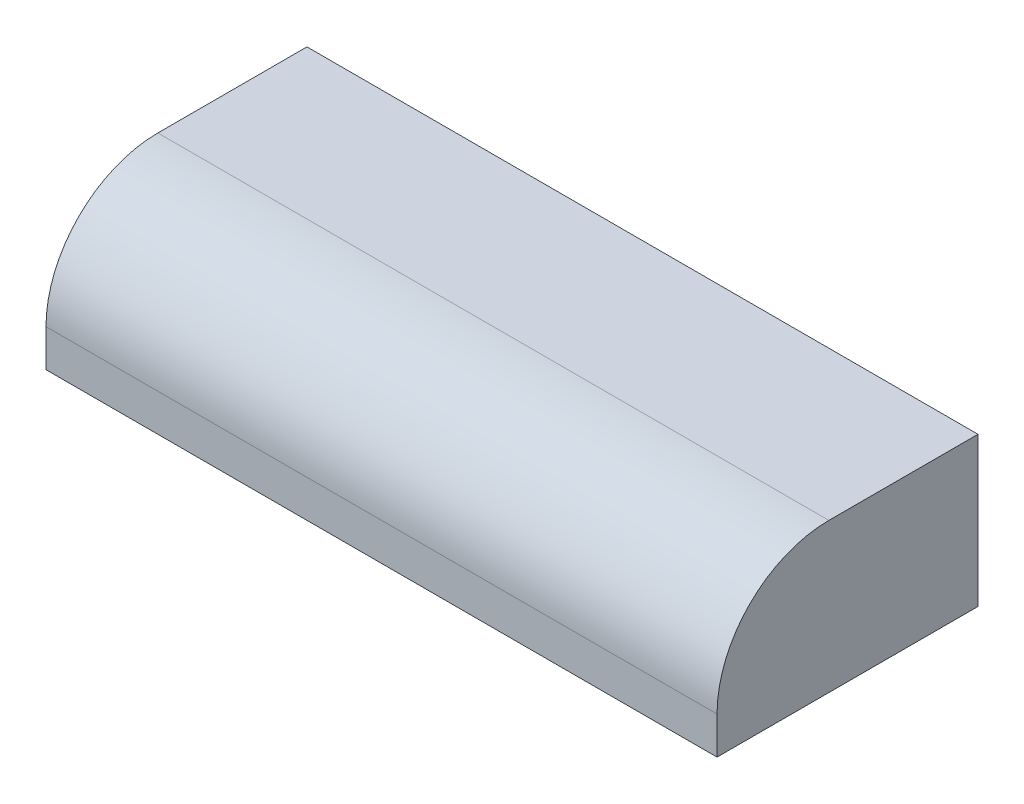
SolidWorks part; units mm, degrees
ref_plane "Front Plane" through (0, 0, 0) normal (0, 0, 1) x (1, 0, 0)
ref_plane "Top Plane" through (0, 0, 0) normal (0, 1, 0) x (1, 0, 0)
ref_plane "Right Plane" through (0, 0, 0) normal (1, 0, 0) x (0, 0, -1)
sketch "Sketch1" plane through (0, 0, 0) normal (1, 0, 0) x (0, 0, -1)
  line L0 (355.6, 203.2) -> (355.6, 0)
  line L1 (355.6, 0) -> (0, 0)
  line L2 (0, 0) -> (0, 203.2)
  line L5 (0, 203.2) -> (355.6, 203.2)
  dimension "D1" = 355.6
  dimension "D4" = 203.2
extrude "Boss-Extrude1" add sketch "Sketch1" along normal blind 914.4
fillet "Fillet1" radius 152.4 1 edges at (457.2, 203.2, 0)
